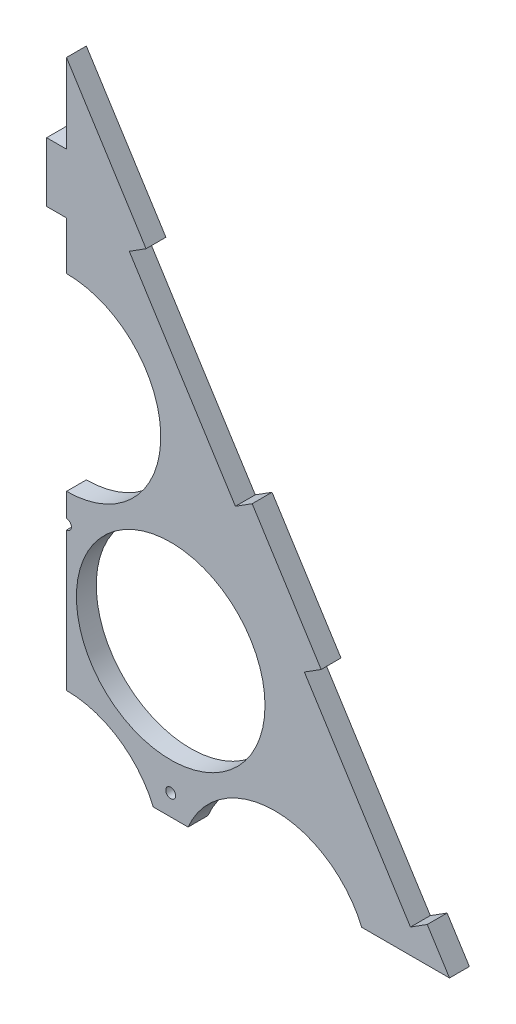
SolidWorks part; units mm, degrees
ref_plane "Plan de face" through (0, 0, 0) normal (0, 0, 1) x (1, 0, 0)
ref_plane "Plan de dessus" through (0, 0, 0) normal (0, 1, 0) x (1, 0, 0)
ref_plane "Plan de droite" through (0, 0, 0) normal (1, 0, 0) x (0, 0, -1)
sketch "Esquisse1" plane through (0, 0, 0) normal (0, 0, 1) x (1, 0, 0)
  line L0 (0, 0) -> (-371.1464, 0) construction
  line L1 (0, 0) -> (478.5179, 0) construction
  line L2 (0, 0) -> (0, 90.9327) construction
  line L3 (0, 90.9327) -> (-157.5, 90.9327) construction
  line L4 (0, 90.9327) -> (157.5, 90.9327) construction
  line L5 (0, 90.9327) -> (0, 181.8653) construction
  line L6 (0, 181.8653) -> (-52.5, 181.8653) construction
  line L7 (0, 181.8653) -> (52.5, 181.8653) construction
  line L8 (0, 181.8653) -> (0, 363.4062) construction
  line L9 (-310, -75.6429) -> (0, 414.5612)
  line L10 (0, 414.5612) -> (310, -75.6429)
  line L11 (310, -75.6429) -> (-310, -75.6429)
  circle A0 centre (-157.5, 0) radius 47.5
  circle A1 centre (-52.5, 0) radius 47.5
  circle A2 centre (52.5, 0) radius 47.5
  circle A3 centre (157.5, 0) radius 47.5
  circle A4 centre (-105, 90.9327) radius 47.5
  circle A5 centre (0, 90.9327) radius 47.5
  circle A6 centre (105, 90.9327) radius 47.5
  circle A7 centre (-52.5, 181.8653) radius 47.5
  circle A8 centre (52.5, 181.8653) radius 47.5
  circle A9 centre (0, 272.798) radius 47.5
  dimension "D1" = 95
  dimension "D2" = 95
  dimension "D3" = 95
  dimension "D4" = 95
  dimension "D5" = 105
  dimension "D6" = 52.5
  dimension "D7" = 52.5
  dimension "D8" = 105
  dimension "D9" = 95
  dimension "D10" = 95
  dimension "D11" = 95
  dimension "D12" = 105
  dimension "D13" = 105
  dimension "D14" = 105
  dimension "D15" = 95
  dimension "D16" = 95
  dimension "D17" = 105
  dimension "D18" = 52.5
  dimension "D19" = 52.5
  dimension "D20" = 95
  dimension "D21" = 105
  dimension "D22" = 80
  dimension "D23" = 620
  dimension "D24" = 580
  dimension "D25" = 0
  dimension "D26" = 580
extrude "Boss.-Extru.1" add sketch "Esquisse1" along normal blind 10
sketch "Esquisse3" plane through (0, 0, 10) normal (0, 0, 1) x (1, 0, 0)
  line L10 (-269.9138, -12.2544) -> (-261.462, -17.5992)
  line L15 (0, 414.5612) -> (-310, -75.6429) construction
  line L16 (-261.462, -17.5992) -> (-208.0137, 66.9187)
  line L17 (-208.0137, 66.9187) -> (-216.4655, 72.2635)
  line L18 (-216.4655, 72.2635) -> (-269.9138, -12.2544)
  line L19 (-181.7241, 127.2002) -> (-173.2723, 121.8554)
  line L20 (-173.2723, 121.8554) -> (-119.8241, 206.3733)
  line L21 (-119.8241, 206.3733) -> (-128.2759, 211.7181)
  line L22 (-128.2759, 211.7181) -> (-181.7241, 127.2002)
  line L23 (-93.5345, 266.6548) -> (-85.0827, 261.31)
  line L24 (-85.0827, 261.31) -> (-31.6344, 345.8279)
  line L25 (-31.6344, 345.8279) -> (-40.0862, 351.1727)
  line L26 (-40.0862, 351.1727) -> (-93.5345, 266.6548)
  line L27 (269.9138, -12.2544) -> (261.462, -17.5992)
  line L28 (310, -75.6429) -> (0, 414.5612) construction
  line L29 (261.462, -17.5992) -> (208.0137, 66.9187)
  line L30 (208.0137, 66.9187) -> (216.4655, 72.2635)
  line L31 (216.4655, 72.2635) -> (269.9138, -12.2544)
  line L32 (181.7241, 127.2002) -> (173.2723, 121.8554)
  line L33 (173.2723, 121.8554) -> (119.8241, 206.3733)
  line L34 (119.8241, 206.3733) -> (128.2759, 211.7181)
  line L35 (128.2759, 211.7181) -> (181.7241, 127.2002)
  line L36 (93.5345, 266.6548) -> (85.0827, 261.31)
  line L37 (85.0827, 261.31) -> (31.6344, 345.8279)
  line L38 (31.6344, 345.8279) -> (40.0862, 351.1727)
  line L39 (40.0862, 351.1727) -> (93.5345, 266.6548)
  line L40 (-310, -75.6429) -> (310, -75.6429) construction
  line L41 (-210, -75.6429) -> (-110, -75.6429)
  line L42 (-210, -75.6429) -> (-210, -65.6429)
  line L43 (-210, -65.6429) -> (-110, -65.6429)
  line L44 (-110, -75.6429) -> (-110, -65.6429)
  line L45 (0, 0) -> (0, -75.6429) construction
  line L46 (210, -65.6429) -> (110, -65.6429)
  line L47 (110, -75.6429) -> (110, -65.6429)
  line L48 (210, -75.6429) -> (110, -75.6429)
  line L49 (210, -75.6429) -> (210, -65.6429)
  dimension "D3" = 100
  dimension "D4" = 10
  dimension "D5" = 100
  dimension "D10" = 10
  dimension "D11" = 100
  dimension "D12" = 10
  dimension "D13" = 100
  dimension "D14" = 10
  dimension "D15" = 100
  dimension "D16" = 75
  dimension "D17" = 75
  dimension "D18" = 65
  dimension "D19" = 100
  dimension "D20" = 10
  dimension "D21" = 10
  dimension "D22" = 100
  dimension "D23" = 75
  dimension "D24" = 65
  dimension "D25" = 100
  dimension "D26" = 10
  dimension "D27" = 75
extrude "Enlèv. mat.-Extru.1" cut sketch "Esquisse3" against normal through all
sketch "Esquisse4" plane through (0, 0, 10) normal (0, 0, 1) x (1, 0, 0)
  line L0 (-110, -65.6429) -> (-210, -65.6429) construction
  circle A0 centre (-157.5, -55.6429) radius 2.5
  circle A3 centre (-52.5, -55.6429) radius 2.5
  circle A4 centre (52.5, -55.6429) radius 2.5
  circle A5 centre (157.5, -55.6429) radius 2.5
  circle A6 centre (-105, 29.0474) radius 2.5
  circle A8 centre (-157.5, 0) radius 47.5 construction
  circle A10 centre (-52.5, 0) radius 47.5 construction
  circle A12 centre (0, 29.0474) radius 2.5
  circle A13 centre (105, 29.0474) radius 2.5
  circle A14 centre (-52.5, 119.98) radius 2.5
  circle A15 centre (-105, 90.9327) radius 47.5 construction
  circle A16 centre (0, 90.9327) radius 47.5 construction
  circle A17 centre (52.5, 119.98) radius 2.5
  circle A18 centre (0, 210.9127) radius 2.5
  circle A19 centre (52.5, 181.8653) radius 47.5 construction
  circle A20 centre (-52.5, 181.8653) radius 47.5 construction
  dimension "D1" = 5
  dimension "D2" = 10
  dimension "D3" = 4
  dimension "D4" = 5
  dimension "D5" = 60
  dimension "D6" = 60
  dimension "D7" = 3
  dimension "D8" = 5
  dimension "D9" = 60
  dimension "D10" = 60
  dimension "D12" = 5
  dimension "D13" = 60
  dimension "D14" = 60
  dimension "D11" = 2
extrude "Enlèv. mat.-Extru.2" cut sketch "Esquisse4" against normal through all
sketch "Esquisse6" plane through (0, 0, 10) normal (0, 0, 1) x (1, 0, 0)
  line L0 (-110, -75.6429) -> (110, -75.6429) construction
  line L1 (-75, -75.6429) -> (75, -75.6429)
  line L2 (-75, -75.6429) -> (-75, -195.6429)
  line L3 (-75, -195.6429) -> (75, -195.6429)
  line L4 (75, -75.6429) -> (75, -195.6429)
  dimension "D1" = 150
  dimension "D2" = 120
  dimension "D3" = 75
extrude "Boss.-Extru.2" add sketch "Esquisse6" against normal blind 10
sketch "Esquisse7" plane through (0, 0, 10) normal (0, 0, 1) x (1, 0, 0)
  line L0 (-75, -75.6429) -> (-75, -195.6429) construction
  line L1 (-75, -110.6429) -> (-65, -110.6429)
  line L2 (-75, -110.6429) -> (-75, -160.6429)
  line L3 (-75, -160.6429) -> (-65, -160.6429)
  line L4 (-65, -110.6429) -> (-65, -160.6429)
  line L5 (-75, -195.6429) -> (75, -195.6429) construction
  line L6 (-25, -195.6429) -> (25, -195.6429)
  line L7 (-25, -195.6429) -> (-25, -186.0721)
  line L8 (-25, -186.0721) -> (25, -186.0721)
  line L9 (25, -195.6429) -> (25, -186.0721)
  line L10 (75, -195.6429) -> (75, -75.6429) construction
  line L11 (75, -160.6429) -> (65, -160.6429)
  line L12 (75, -160.6429) -> (75, -110.6429)
  line L13 (75, -110.6429) -> (65, -110.6429)
  line L14 (65, -160.6429) -> (65, -110.6429)
  line L15 (75, -75.6429) -> (110, -75.6429) construction
  line L16 (-110, -75.6429) -> (-75, -75.6429) construction
  dimension "D1" = 10
  dimension "D2" = 10
  dimension "D3" = 50
  dimension "D4" = 50
  dimension "D5" = 35
  dimension "D6" = 35
  dimension "D7" = 50
  dimension "D8" = 50
extrude "Enlèv. mat.-Extru.3" cut sketch "Esquisse7" against normal blind 10
sketch "Esquisse10" plane through (0, 0, 10) normal (0, 0, 1) x (1, 0, 0)
  line L0 (0, 414.5612) -> (0, 109.4612)
  line L1 (0, 109.4612) -> (337.1066, 109.4612)
  line L2 (337.1066, 109.4612) -> (337.1066, -228.0526)
  line L3 (337.1066, -228.0526) -> (-388.9691, -228.0526)
  line L4 (-388.9691, -228.0526) -> (-388.9691, 414.5612)
  line L5 (-388.9691, 414.5612) -> (0, 414.5612)
  dimension "D1" = 305.1
extrude "Enlèv. mat.-Extru.5" cut sketch "Esquisse10" against normal blind 10
sketch "Esquisse11" plane through (0, 0, 10) normal (0, 0, 1) x (1, 0, 0)
  line L0 (0, 320.298) -> (0, 414.5612) construction
  line L1 (0, 374.5612) -> (-10, 374.5612)
  line L2 (0, 374.5612) -> (0, 344.5612)
  line L3 (0, 344.5612) -> (-10, 344.5612)
  line L4 (-10, 374.5612) -> (-10, 344.5612)
  dimension "D1" = 10
  dimension "D2" = 30
  dimension "D3" = 40
extrude "Boss.-Extru.4" add sketch "Esquisse11" against normal blind 10
